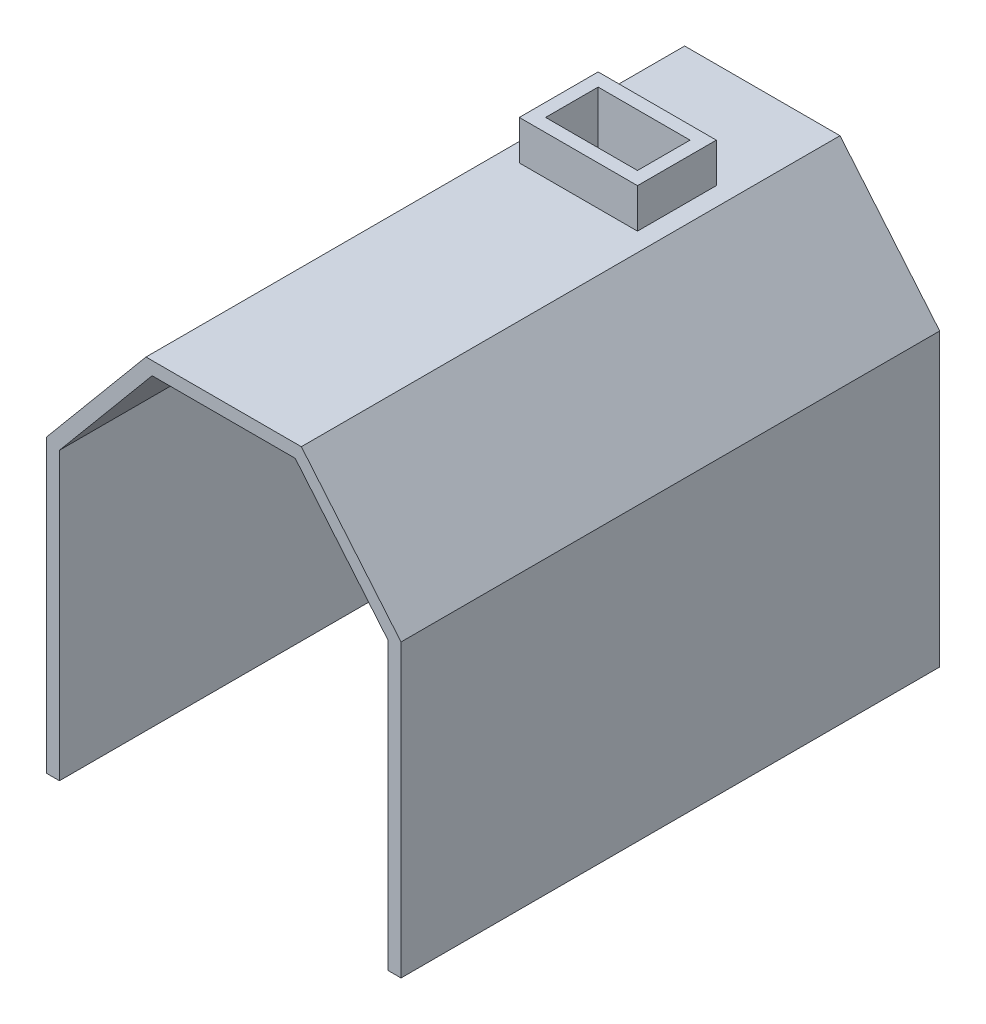
SolidWorks part; units mm, degrees
ref_plane "Front Plane" through (0, 0, 0) normal (0, 0, 1) x (1, 0, 0)
ref_plane "Top Plane" through (0, 0, 0) normal (0, 1, 0) x (1, 0, 0)
ref_plane "Right Plane" through (0, 0, 0) normal (1, 0, 0) x (0, 0, -1)
sketch "Sketch1" plane through (0, 0, 0) normal (0, 0, 1) x (1, 0, 0)
  line L0 (-125, 108.94) -> (-54.45, 193.35)
  line L2 (125, 108.94) -> (125, -108.94)
  line L4 (-125, 108.94) -> (-125, -108.94)
  line L5 (-54.45, 193.35) -> (54.45, 193.35)
  line L6 (-135, 112.5687) -> (-59.1249, 203.35)
  line L7 (125, 108.94) -> (54.45, 193.35)
  line L8 (-59.1249, 203.35) -> (59.1249, 203.35)
  line L9 (135, 112.5687) -> (59.1249, 203.35)
  line L10 (135, 112.5687) -> (135, -108.94)
  line L12 (-135, 112.5687) -> (-135, -108.94)
  line L16 (135, -118.94) -> (-135, -118.94) construction
  line L17 (125, -108.94) -> (-125, -108.94) construction
  line L18 (-135, -108.94) -> (-125, -108.94)
  line L19 (125, -108.94) -> (135, -108.94)
  line L20 (-135, 112.5687) -> (-135, -118.94) construction
  line L21 (135, 112.5687) -> (135, -118.94) construction
  point P0 (0, 0)
  dimension "D1" = 217.88
  dimension "D2" = 250
  dimension "D3" = 84.41
  dimension "D4" = 70.55
  dimension "D5" = 84.41
  dimension "D6" = 70.55
  dimension "D7" = 10
extrude "Boss-Extrude1" add sketch "Sketch1" along normal mid plane 410
sketch "Sketch2" plane through (0, 0, 0) normal (0, 1, 0) x (1, 0, 0)
  line L1 (34.975, 115) -> (-34.975, 115)
  line L2 (34.975, 115) -> (34.975, 75)
  line L3 (34.975, 75) -> (-34.975, 75)
  line L4 (-34.975, 115) -> (-34.975, 75)
  line L5 (34.975, 115) -> (-34.975, 75) construction
  line L6 (34.975, 75) -> (-34.975, 115) construction
  line L8 (59.1249, -205) -> (-59.1249, -205) construction
  point P0 (0, 95)
  dimension "D1" = 300
  dimension "D2" = 40
extrude "Cut-Extrude1" cut sketch "Sketch2" along normal through all
sketch "Sketch3" plane through (0, 0, 0) normal (0, 1, 0) x (1, 0, 0)
  line L0 (44.975, 125) -> (-44.975, 125)
  line L1 (-44.975, 125) -> (-44.975, 65)
  line L2 (-44.975, 65) -> (44.975, 65)
  line L3 (44.975, 65) -> (44.975, 125)
  line L4 (34.975, 115) -> (-34.975, 115)
  line L5 (-34.975, 115) -> (-34.975, 75)
  line L6 (-34.975, 75) -> (34.975, 75)
  line L7 (34.975, 75) -> (34.975, 115)
  line L8 (34.975, 115) -> (-34.975, 115)
  line L9 (-34.975, 115) -> (-34.975, 75)
  line L10 (-34.975, 75) -> (34.975, 75)
  line L11 (34.975, 75) -> (34.975, 115)
  dimension "D1" = 0
  dimension "D2" = 10
extrude "Boss-Extrude2" add sketch "Sketch3" along normal blind 30 from surface at 203.35 starting at face at (0, 203.35, 0)
